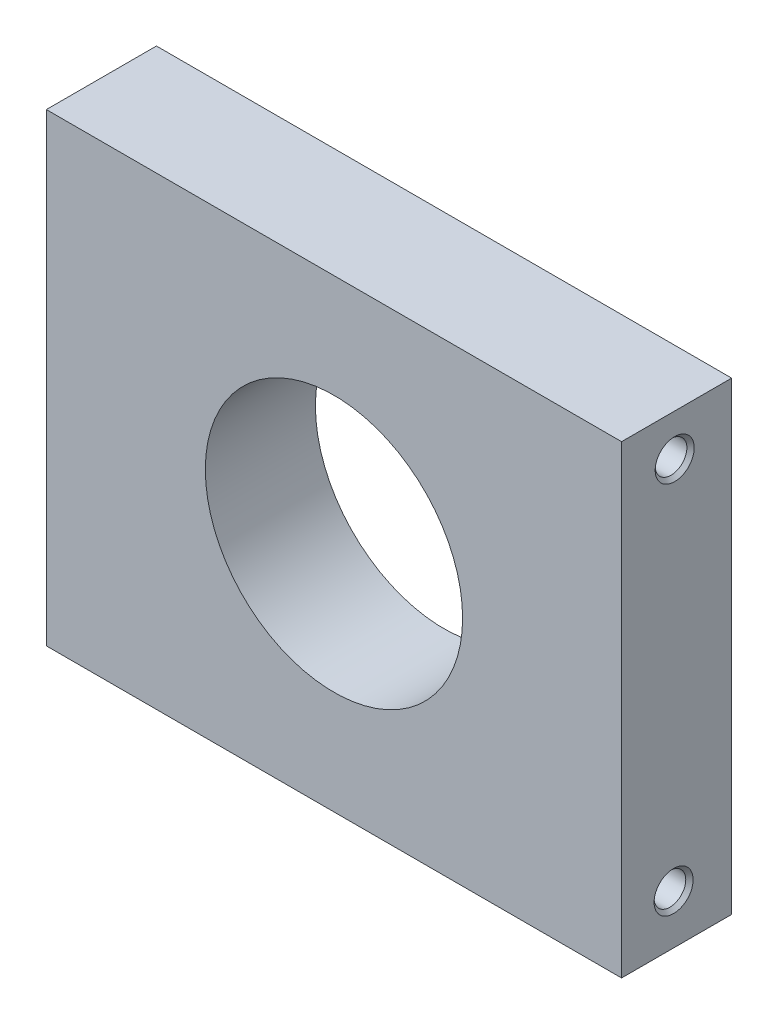
SolidWorks part; units mm, degrees
ref_plane "Front Plane" through (0, 0, 0) normal (0, 0, 1) x (1, 0, 0)
ref_plane "Top Plane" through (0, 0, 0) normal (0, 1, 0) x (1, 0, 0)
ref_plane "Right Plane" through (0, 0, 0) normal (1, 0, 0) x (0, 0, -1)
sketch "Sketch1" plane through (0, 0, 0) normal (0, 0, 1) x (1, 0, 0)
  line L1 (-49.7745, 40.1931) -> (49.7745, 40.1931)
  line L2 (-49.7745, 40.1931) -> (-49.7745, -40.1931)
  line L3 (-49.7745, -40.1931) -> (49.7745, -40.1931)
  line L4 (49.7745, 40.1931) -> (49.7745, -40.1931)
  line L5 (-49.7745, 40.1931) -> (49.7745, -40.1931) construction
  line L6 (-49.7745, -40.1931) -> (49.7745, 40.1931) construction
  point P0 (0, 0)
  dimension "D1" = 80.3863
  dimension "D2" = 99.5491
extrude "Extrude2" add sketch "Sketch1" along normal blind 19.05
sketch "Sketch2" plane through (0, 0, 19.05) normal (0, 0, 1) x (1, 0, 0)
  circle A0 centre (0, 0) radius 22.2631
  dimension "D1" = 44.5262
extrude "Extrude3" cut sketch "Sketch2" against normal through all
hole_wizard "#12-24 Tapped Hole1" positions "3DSketch1" profile "Sketch3" tap size "#12-24" standard "Ansi Inch" end condition through all
sketch3d "3DSketch1"
  point P0 (49.7745, 32.985, 9.8572)
  point P2 (49.7745, -31.6561, 10.0471)
sketch "Sketch3" plane through (49.7745, 32.985, 9.8572) normal (0, 1, 0) x (0, 0, -1)
  line L0 (0, 0) -> (0, 99.5491)
  line L1 (0, 99.5491) -> (2.7432, 99.5491)
  line L2 (2.7432, 99.5491) -> (2.7432, 0.635)
  line L3 (2.7432, 0.635) -> (3.3782, 0)
  line L5 (3.3782, 0) -> (0, 0)
  line L6 (-2.7432, 0.635) -> (-3.3782, 0) construction
  line L11 (0, -6.35) -> (0, 107.95) construction
  dimension "Thread Major Dia." = 5.4864
  dimension "Thru Tap Drill Depth" = 99.5491
  dimension "Near C'Sink Dia." = 6.7564
  dimension "Near C'Sink Angle" = 90
